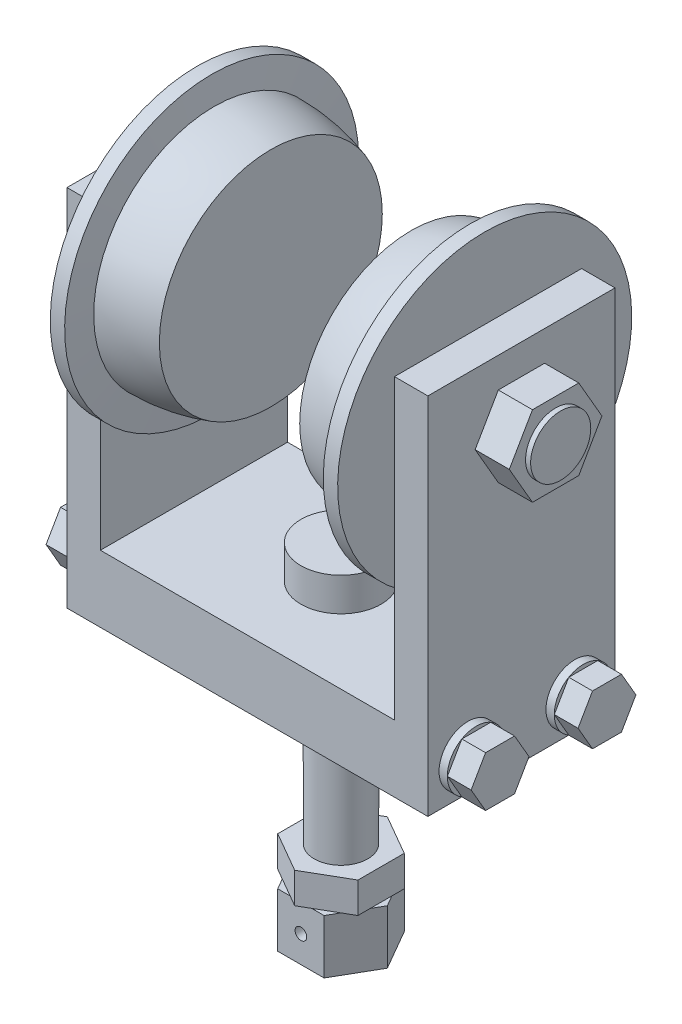
SolidWorks part; units mm, degrees
ref_plane "Front" through (0, 0, 0) normal (0, 0, 1) x (1, 0, 0)
ref_plane "Top" through (0, 0, 0) normal (0, 1, 0) x (1, 0, 0)
ref_plane "Right" through (0, 0, 0) normal (1, 0, 0) x (0, 0, -1)
ref_plane "Z PLANE" through (0, 0, 0) normal (0, 0, 1) x (1, 0, 0)
ref_plane "YOKE BOTTOM" through (0, 0, 0) normal (0, 1, 0) x (-1, 0, 0)
ref_plane "X PLANE" through (0, 0, 0) normal (1, 0, 0) x (0, 0, -1)
sketch "YOKE CROSS SECTION" plane through (0, 0, 0) normal (1, 0, 0) x (0, 0, -1)
  line L0 (0, 0) -> (0, 57.0916) construction
  line L1 (0, 84.8167) -> (0, -84.8167) construction
  line L2 (-44.45, 0) -> (44.45, 0)
  line L3 (69.1602, 0) -> (-69.1602, 0) construction
  line L4 (44.45, 0) -> (44.45, 31.75)
  line L5 (-44.45, 0) -> (-44.45, 31.75)
  line L6 (44.45, 31.75) -> (-44.45, 31.75)
  point P12 (0, 31.75)
  dimension "D1" = 31.75
  dimension "D2" = 88.9
ref_plane "1/2 YOKE LENGTH (A)" through (69.85, 0, 0) normal (1, 0, 0) x (0, 0, -1)
extrude "YOKE" add sketch "YOKE CROSS SECTION" along normal up to surface (69.85 mm away) up to plane "1/2 YOKE LENGTH (A)"
sketch "SIDEPLATE PROFILE" plane through (69.85, 0, 0) normal (1, 0, 0) x (0, 0, -1)
  line L0 (0, 0) -> (0, 74.7424) construction
  line L1 (0, 85.6885) -> (0, -85.6885) construction
  line L2 (-44.45, 0) -> (44.45, 0)
  line L3 (44.45, 0) -> (44.45, 173.0375)
  line L4 (-44.45, 0) -> (-44.45, 173.0375)
  line L5 (44.45, 173.0375) -> (-44.45, 173.0375)
  point P11 (0, 173.0375)
  dimension "D1" = 173.0375
ref_plane "WHEEL HEIGHT" through (0, 139.7, 0) normal (0, 1, 0) x (-1, 0, 0)
ref_plane "SCREW LOCATION X" through (0, 0, 25.4) normal (0, 0, 1) x (1, 0, 0)
ref_plane "SCREW LOCATION Y" through (0, 15.875, 0) normal (0, 1, 0) x (-1, 0, 0)
extrude "SIDEPLATE" add sketch "SIDEPLATE PROFILE" along normal blind 15.875
sketch "WHEEL PIN NUT PROFILE" plane through (85.725, 0, 0) normal (1, 0, 0) x (0, 0, -1)
  line L0 (0, 85.6885) -> (0, -85.6885) construction
  line L1 (21.997, 139.7) -> (10.9985, 158.75)
  line L2 (10.9985, 158.75) -> (-10.9985, 158.75)
  line L3 (-10.9985, 158.75) -> (-21.997, 139.7)
  line L4 (-21.997, 139.7) -> (-10.9985, 120.65)
  line L5 (-10.9985, 120.65) -> (10.9985, 120.65)
  line L6 (10.9985, 120.65) -> (21.997, 139.7)
  line L7 (69.1602, 139.7) -> (-69.1602, 139.7) construction
  circle A0 centre (0, 139.7) radius 19.05 construction
  dimension "D1" = 38.1
extrude "WHEEL PIN NUT" add sketch "WHEEL PIN NUT PROFILE" along normal blind 16.2306
sketch "WHEEL PIN PROJECTION PROFILE" plane through (101.9556, 0, 0) normal (1, 0, 0) x (0, 0, -1)
  line L0 (0, 85.6885) -> (0, -85.6885) construction
  line L1 (69.1602, 139.7) -> (-69.1602, 139.7) construction
  circle A0 centre (0, 139.7) radius 14.2875
  dimension "D1" = 28.575
extrude "WHEEL PIN PROJECTION" add sketch "WHEEL PIN PROJECTION PROFILE" along normal blind 2.413
sketch "LOCKNUTS PROFILE" plane through (85.725, 0, 0) normal (1, 0, 0) x (0, 0, -1)
  line L0 (-25.4, 84.8167) -> (-25.4, -84.8167) construction
  line L1 (50, 15.875) -> (-50, 15.875) construction
  circle A0 centre (-25.4, 15.875) radius 13.7541
  dimension "D1" = 27.5082
extrude "LOCKNUTS" add sketch "LOCKNUTS PROFILE" along normal blind 3.9624
sketch "SCREWS PROFILE" plane through (89.6874, 0, 0) normal (1, 0, 0) x (0, 0, -1)
  line L0 (50, 15.875) -> (-50, 15.875) construction
  line L1 (-11.6518, 15.875) -> (-18.5259, 27.7812)
  line L2 (-18.5259, 27.7812) -> (-32.2741, 27.7812)
  line L3 (-32.2741, 27.7812) -> (-39.1482, 15.875)
  line L4 (-39.1482, 15.875) -> (-32.2741, 3.9688)
  line L5 (-32.2741, 3.9688) -> (-18.5259, 3.9688)
  line L6 (-18.5259, 3.9688) -> (-11.6518, 15.875)
  line L7 (-25.4, 84.8167) -> (-25.4, -84.8167) construction
  circle A0 centre (-25.4, 15.875) radius 11.9062 construction
  dimension "D1" = 23.8125
extrude "SCREWS" add sketch "SCREWS PROFILE" along normal blind 11.2776
sketch "PROFILE" plane through (0, 31.75, 0) normal (0, 1, 0) x (-1, 0, 0)
  line L0 (85.6885, 0) -> (-85.6885, 0) construction
  line L1 (0, 82.9507) -> (0, -82.9507) construction
  circle A0 centre (0, 0) radius 19.05
  dimension "D1" = 38.1
extrude "KING BOLT HEAD" add sketch "PROFILE" along normal blind 15.875
mirror "Mirror1" about plane through (0, 0, 0) normal (0, 0, 1) of "SCREWS", "LOCKNUTS"
mirror "Mirror5" about plane through (0, 0, 0) normal (1, 0, 0) of bodies 112
ref_plane "TOP OF NUT" through (0, -76.2, 0) normal (0, 1, 0) x (-1, 0, 0)
sketch "DIA." plane through (0, 0, 0) normal (0, -1, 0) x (1, 0, 0)
  line L0 (85.6885, 0) -> (-85.6885, 0) construction
  line L1 (0, -82.9507) -> (0, 82.9507) construction
  circle A0 centre (0, 0) radius 12.7
  dimension "D1" = 25.4
extrude "KING BOLT" add sketch "DIA." along normal up to surface (76.2 mm away) up to plane "TOP OF NUT"
sketch "KING BOLT JAN NUT PROFILE" plane through (0, -76.2, 0) normal (0, -1, 0) x (1, 0, 0)
  line L0 (85.6885, 0) -> (-85.6885, 0) construction
  line L1 (0, -21.997) -> (19.05, -10.9985)
  line L2 (19.05, -10.9985) -> (19.05, 10.9985)
  line L3 (19.05, 10.9985) -> (0, 21.997)
  line L4 (0, 21.997) -> (-19.05, 10.9985)
  line L5 (-19.05, 10.9985) -> (-19.05, -10.9985)
  line L6 (-19.05, -10.9985) -> (0, -21.997)
  line L7 (0, -82.9507) -> (0, 82.9507) construction
  circle A0 centre (0, 0) radius 19.05 construction
  dimension "D1" = 38.1
extrude "KING BOLT JAM NUT" add sketch "KING BOLT JAN NUT PROFILE" along normal blind 14.605
sketch "KING BOLT NUT PROFILE" plane through (0, -90.805, 0) normal (0, -1, 0) x (1, 0, 0)
  line L1 (21.997, 0) -> (10.9985, 19.05)
  line L2 (10.9985, 19.05) -> (-10.9985, 19.05)
  line L3 (-10.9985, 19.05) -> (-21.997, 0)
  line L4 (-21.997, 0) -> (-10.9985, -19.05)
  line L5 (-10.9985, -19.05) -> (10.9985, -19.05)
  line L6 (10.9985, -19.05) -> (21.997, 0)
  line L10 (0, -82.9507) -> (0, 82.9507) construction
  line L11 (85.6885, 0) -> (-85.6885, 0) construction
  circle A0 centre (0, 0) radius 19.05 construction
  dimension "D1" = 38.1
extrude "KING BOLT NUT" add sketch "KING BOLT NUT PROFILE" along normal blind 25.7048
sketch "Sketch5" plane through (0, -116.5098, 0) normal (0, -1, 0) x (1, 0, 0)
  circle A0 centre (0, 0) radius 12.7 construction
  circle A1 centre (0, 0) radius 12.7
extrude "EXTENDED KING BOLT" add sketch "Sketch5" along normal blind 6.35
chamfer "Chamfer1" distance 2.3812 angle 45 1 edges at (0, -122.8598, -12.7)
ref_plane "MOUNTING REF PLANE" through (0, -34.925, 0) normal (0, 1, 0) x (-1, 0, 0)
sketch "Sketch7" plane through (0, 0, 0) normal (0, 0, 1) x (1, 0, 0)
  line L0 (68.2625, 155.575) -> (68.2625, 209.55)
  line L1 (60.325, 196.85) -> (61.4361, 209.55)
  line L2 (33.3375, 139.7) -> (33.3375, 192.6547)
  line L3 (69.85, 139.7) -> (33.3375, 139.7)
  line L4 (69.85, 155.575) -> (69.85, 139.7)
  line L5 (69.85, 155.575) -> (68.2625, 155.575)
  line L6 (68.2625, 209.55) -> (61.4361, 209.55)
  line L7 (69.85, -75.0522) -> (69.85, 75.0522) construction
  arc A0 (60.325, 196.85) -> (33.3375, 192.6547) centre (60.325, 107.95) ccw
  dimension "D3" = 88.9
  dimension "D1" = 31.75
  dimension "D2" = 9.525
  dimension "D4" = 15.875
  dimension "D5" = 1.5875
  dimension "D6" = 6.8264
  dimension "D7" = 69.85
  dimension "D8" = 12.7
  dimension "D9" = 52.9547
revolve "WHEEL" add sketch "Sketch7" angle 360 about L3
mirror "Mirror6" about plane through (0, 0, 0) normal (1, 0, 0) of "WHEEL"
sketch "Sketch8" plane through (0, 0, 19.05) normal (0, 0, 1) x (1, 0, 0)
  line L0 (0, -82.9507) -> (0, 82.9507) construction
  line L1 (-10.9985, -116.5098) -> (-21.997, -116.5098) construction
  circle A0 centre (0, -103.8098) radius 2.7686
  dimension "D1" = 5.5372
  dimension "D2" = 12.7
extrude "COTTER PIN HOLE" cut sketch "Sketch8" against normal up to next
sketch "Sketch9" plane through (0, 0, 0) normal (0, -1, 0) x (1, 0, 0)
  circle A0 centre (0, 0) radius 25.4
  circle A1 centre (0, 0) radius 30.1625
  dimension "D1" = 50.8
  dimension "D2" = 60.325
extrude "SPACER" [suppressed] add sketch "Sketch9" along normal blind 12.7
ref_plane "TREAD OF TRACK" through (0, 82.55, 0) normal (0, 1, 0) x (-1, 0, 0)
